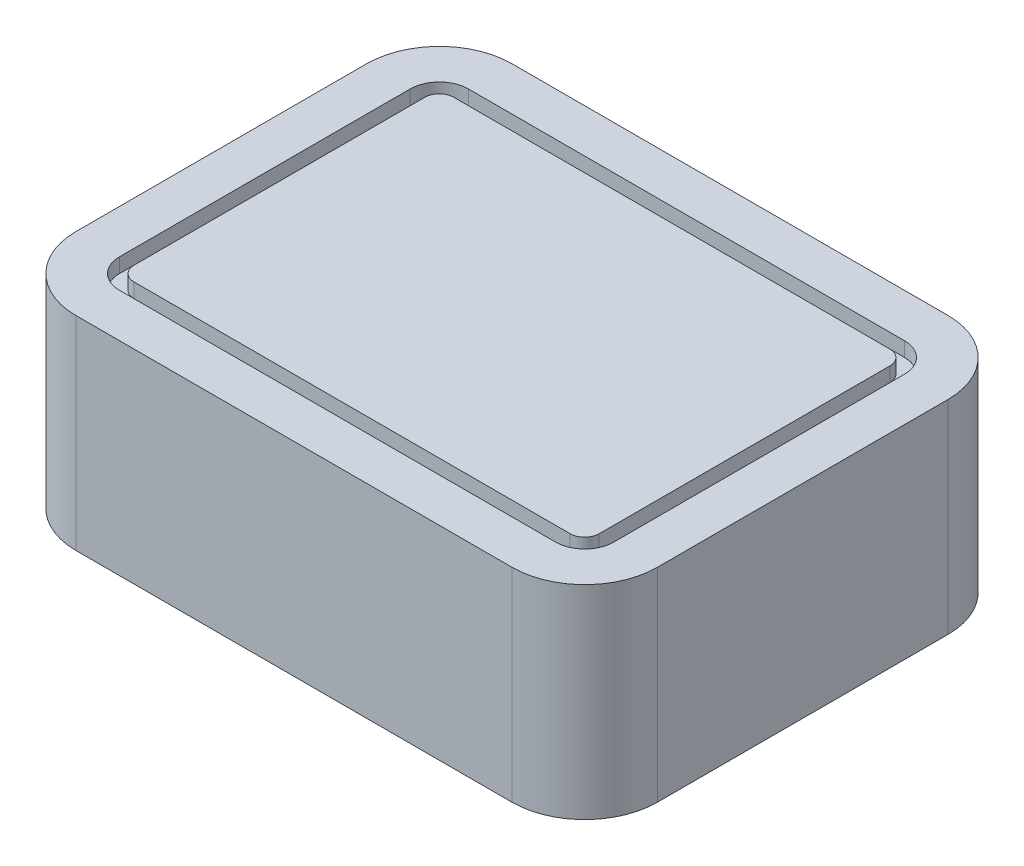
SolidWorks part; units mm, degrees
ref_plane "Front Plane" through (0, 0, 0) normal (0, 0, 1) x (1, 0, 0)
ref_plane "Top Plane" through (0, 0, 0) normal (0, 1, 0) x (1, 0, 0)
ref_plane "Right Plane" through (0, 0, 0) normal (1, 0, 0) x (0, 0, -1)
sketch "Sketch1" plane through (0, 0, 0) normal (0, 1, 0) x (1, 0, 0)
  line L1 (-20, 15) -> (20, 15)
  line L2 (-20, 15) -> (-20, -15)
  line L3 (-20, -15) -> (20, -15)
  line L4 (20, 15) -> (20, -15)
  line L5 (-20, 15) -> (20, -15) construction
  line L6 (-20, -15) -> (20, 15) construction
  point P0 (0, 0)
  dimension "D1" = 30
  dimension "D2" = 40
extrude "Boss-Extrude1" add sketch "Sketch1" along normal blind 14
fillet "Fillet1" radius 5 4 edges at (-20, 7, -15) (-20, 7, 15) (20, 7, -15) (20, 7, 15)
sketch "Sketch2" plane through (0, 14, 0) normal (0, 1, 0) x (1, 0, 0)
  line L8 (15, 12) -> (-15, 12)
  line L9 (-17, 10) -> (-17, -10)
  line L10 (-15, -12) -> (15, -12)
  line L11 (17, -10) -> (17, 10)
  line L12 (15, 12) -> (-15, 12)
  line L13 (-17, 10) -> (-17, -10)
  line L14 (-15, -12) -> (15, -12)
  line L15 (17, -10) -> (17, 10)
  line L20 (15, 11) -> (-15, 11)
  line L21 (-16, 10) -> (-16, -10)
  line L22 (-15, -11) -> (15, -11)
  line L23 (16, -10) -> (16, 10)
  line L24 (15, 11) -> (-15, 11)
  line L25 (-16, 10) -> (-16, -10)
  line L26 (-15, -11) -> (15, -11)
  line L27 (16, -10) -> (16, 10)
  arc A8 (-15, 12) -> (-17, 10) centre (-15, 10) ccw
  arc A9 (-17, -10) -> (-15, -12) centre (-15, -10) ccw
  arc A10 (15, -12) -> (17, -10) centre (15, -10) ccw
  arc A11 (17, 10) -> (15, 12) centre (15, 10) ccw
  arc A12 (-15, 12) -> (-17, 10) centre (-15, 10) ccw
  arc A13 (-17, -10) -> (-15, -12) centre (-15, -10) ccw
  arc A14 (15, -12) -> (17, -10) centre (15, -10) ccw
  arc A15 (17, 10) -> (15, 12) centre (15, 10) ccw
  arc A20 (-15, 11) -> (-16, 10) centre (-15, 10) ccw
  arc A21 (-15, 11) -> (-16, 10) centre (-15, 10) ccw
  arc A22 (-16, -10) -> (-15, -11) centre (-15, -10) ccw
  arc A23 (-16, -10) -> (-15, -11) centre (-15, -10) ccw
  arc A24 (15, -11) -> (16, -10) centre (15, -10) ccw
  arc A25 (15, -11) -> (16, -10) centre (15, -10) ccw
  arc A26 (16, 10) -> (15, 11) centre (15, 10) ccw
  arc A27 (16, 10) -> (15, 11) centre (15, 10) ccw
  dimension "D1" = 3
  dimension "D2" = 4
extrude "Cut-Extrude1" cut sketch "Sketch2" against normal blind 1
